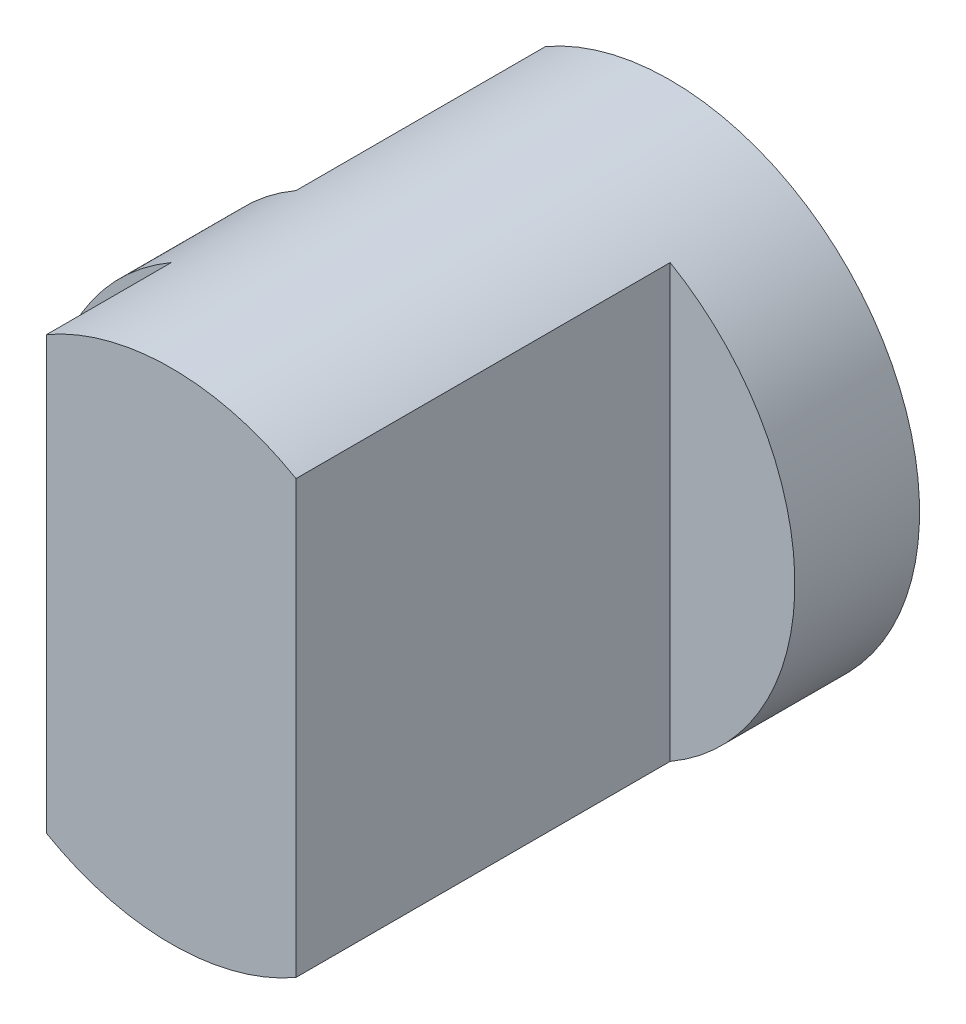
SolidWorks part; units mm, degrees
ref_plane "Front" through (0, 0, 0) normal (0, 0, 1) x (1, 0, 0)
ref_plane "Top" through (0, 0, 0) normal (0, 1, 0) x (1, 0, 0)
ref_plane "Right" through (0, 0, 0) normal (1, 0, 0) x (0, 0, -1)
sketch "Sketch1" plane through (0, 0, 0) normal (0, 0, 1) x (1, 0, 0)
  circle A0 centre (0, 0) radius 2
  dimension "D1" = 4
extrude "Boss-Extrude1" add sketch "Sketch1" along normal blind 4
sketch "Sketch2" plane through (0, 0, 0) normal (0, 1, 0) x (1, 0, 0)
  line L1 (2, -4) -> (1, -4)
  line L2 (2, -4) -> (2, -1)
  line L3 (2, -1) -> (1, -1)
  line L4 (1, -4) -> (1, -1)
  line L5 (-2, -4) -> (-1, -4)
  line L6 (-2, -4) -> (-2, -3)
  line L7 (-2, -3) -> (-1, -3)
  line L8 (-1, -4) -> (-1, -3)
  line L9 (-2, 0) -> (-1, 0)
  line L10 (-2, 0) -> (-2, -2)
  line L11 (-2, -2) -> (-1, -2)
  line L12 (-1, 0) -> (-1, -2)
  dimension "D1" = 1
  dimension "D2" = 1
  dimension "D3" = 1
  dimension "D4" = 3
  dimension "D5" = 2
extrude "Cut-Extrude1" cut sketch "Sketch2" against normal mid plane 10
